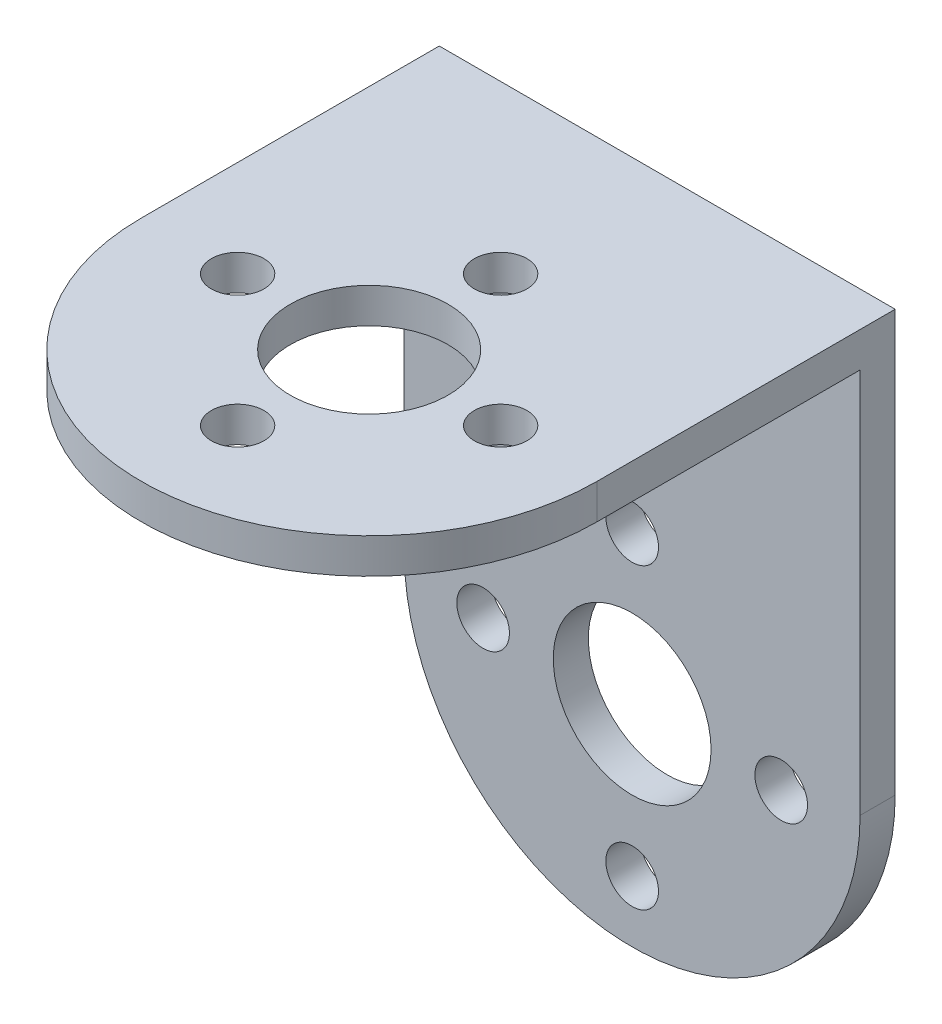
SolidWorks part; units mm, degrees
material "AISI 4340 Steel, annealed"
ref_plane "Front Plane" through (0, 0, 0) normal (0, 0, 1) x (1, 0, 0)
ref_plane "Top Plane" through (0, 0, 0) normal (0, 1, 0) x (1, 0, 0)
ref_plane "Right Plane" through (0, 0, 0) normal (1, 0, 0) x (0, 0, -1)
sketch "Sketch2" plane through (0, 0, 0) normal (1, 0, 0) x (0, 0, -1)
  line L0 (-15.5, 1) -> (14.5, 1)
  line L1 (14.5, 1) -> (14.5, -36)
  line L2 (14.5, -36) -> (12.5, -36)
  line L3 (12.5, -36) -> (12.5, -1)
  line L4 (12.5, -1) -> (-15.5, -1)
  line L5 (-15.5, -1) -> (-15.5, 1)
  dimension "D1" = 1
  dimension "D2" = 2
  dimension "D3" = 2
  dimension "D4" = 30
  dimension "D5" = 15.5
  dimension "D6" = 37
extrude "Boss-Extrude1" add sketch "Sketch2" along normal blind 26
sketch "Sketch4" plane through (0, 0, -12.5) normal (0, 0, 1) x (1, 0, 0)
  line L0 (13, -1) -> (13, -27.3709) construction
  line L1 (0, -24) -> (26, -24) construction
  line L3 (26, 1) -> (0, 1) construction
  line L4 (0, -1) -> (0, -36)
  line L5 (0, -36) -> (26, -36)
  line L6 (26, -36) -> (26, -1)
  line L7 (26, -1) -> (0, -1)
  line L8 (0, -1) -> (0, -36)
  line L9 (0, -36) -> (26, -36)
  line L10 (26, -36) -> (26, -1)
  line L11 (26, -1) -> (0, -1)
  arc A1 (0, -23) -> (26, -23) centre (13, -23) ccw
  circle A2 centre (13, -24) radius 4.5
  circle A3 centre (4.5, -24) radius 1.5
  circle A7 centre (13, -15.5) radius 1.5
  circle A8 centre (21.5, -24) radius 1.5
  circle A9 centre (13, -32.5) radius 1.5
  point P24 (6.25, -15.25)
  point P25 (13, -24)
  line M6 (0, -36) -> (26, -36)
  line M7 (26, -36) -> (26, -1)
  dimension "D2" = 13
  dimension "D3" = 9
  dimension "D4" = 3
  dimension "D5" = 8.5
  dimension "D7" = 17
  dimension "D8" = 8.5
  dimension "D9" = 25
  dimension "D1" = 0
  dimension "D6" = 4
extrude "Cut-Extrude2" cut sketch "Sketch4" against normal through all contours A2 | A3 | A9 | A8 | A7 | A1 L8 M6 | A1 L9 M7
sketch "Sketch5" plane through (0, -1, 0) normal (0, -1, 0) x (1, 0, 0)
  line L0 (13, 15.5) -> (13, -12.2002) construction
  line L1 (-7.0706, 2.5) -> (33.0706, 2.5) construction
  line L2 (0, 15.5) -> (0, -12.5) construction
  line L4 (0, 15.5) -> (0, -12.5)
  line L5 (0, -12.5) -> (26, -12.5)
  line L6 (26, -12.5) -> (26, 15.5)
  line L7 (26, 15.5) -> (0, 15.5)
  line L8 (0, 15.5) -> (0, -12.5)
  line L9 (0, -12.5) -> (26, -12.5)
  line L10 (26, -12.5) -> (26, 15.5)
  line L11 (26, 15.5) -> (0, 15.5)
  arc A0 (26, 2.5) -> (0, 2.5) centre (13, 2.5) ccw
  circle A1 centre (13, 2.5) radius 4.5
  circle A2 centre (13, 10) radius 1.5
  circle A3 centre (20.5, 2.5) radius 1.5
  circle A4 centre (13, -5) radius 1.5
  circle A5 centre (5.5, 2.5) radius 1.5
  point P11 (13, 2.5)
  point P24 (13, 2.5)
  line M6 (0, 15.5) -> (0, -12.5)
  line M9 (26, 15.5) -> (0, 15.5)
  dimension "D2" = 9
  dimension "D3" = 3
  dimension "D8" = 7.5
  dimension "D9" = 3
  dimension "D4" = 15
  dimension "D6" = 15
  dimension "D5" = 15
  dimension "D7" = 7.5
  dimension "D1" = 0
extrude "Cut-Extrude3" cut sketch "Sketch5" against normal through all contours A5 | A4 | A1 | A3 | A0 L11 M6 | A0 L10 M9 | A2
sketch "Sketch6" plane through (0, -1, 0) normal (0, -1, 0) x (1, 0, 0)
  line L3 (0, 2.5) -> (0, -12.5)
  line L4 (0, -12.5) -> (26, -12.5)
  line L5 (26, -12.5) -> (26, 2.5)
  line L6 (0, 2.5) -> (0, -12.5)
  line L7 (0, -12.5) -> (26, -12.5)
  line L8 (26, -12.5) -> (26, 2.5)
  circle A0 centre (5.5, 2.5) radius 1.5 construction
  arc A1 (26, 2.5) -> (0, 2.5) centre (13, 2.5) ccw
  arc A2 (26, 2.5) -> (0, 2.5) centre (13, 2.5) ccw
  circle A3 centre (13, 10) radius 1.5 construction
  circle A4 centre (20.5, 2.5) radius 1.5 construction
  circle A5 centre (13, -5) radius 1.5 construction
  circle A6 centre (13, -5) radius 1.5
  circle A7 centre (20.5, 2.5) radius 1.5
  circle A8 centre (13, 10) radius 1.5
  circle A9 centre (5.5, 2.5) radius 1.5
  dimension "D1" = 0
